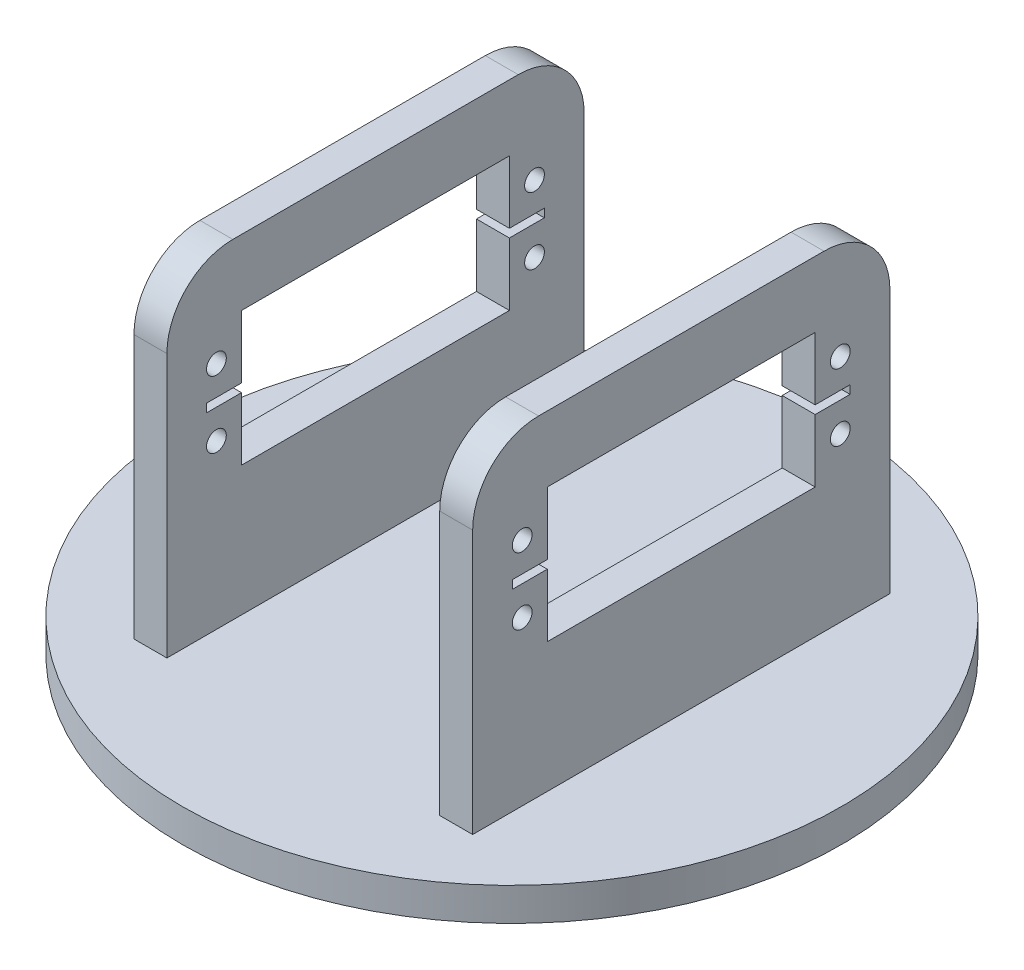
SolidWorks part; units mm, degrees
ref_plane "Front Plane" through (0, 0, 0) normal (0, 0, 1) x (1, 0, 0)
ref_plane "Top Plane" through (0, 0, 0) normal (0, 1, 0) x (1, 0, 0)
ref_plane "Right Plane" through (0, 0, 0) normal (1, 0, 0) x (0, 0, -1)
sketch "Sketch1" plane through (0, 0, 0) normal (0, 1, 0) x (1, 0, 0)
  circle A0 centre (0, 0) radius 50
  circle A1 centre (0, 0) radius 2.778
  dimension "D1" = 100
  dimension "D2" = 5.556
extrude "Boss-Extrude1" add sketch "Sketch1" along normal mid plane 5
sketch "Sketch2" plane through (0, 2.5, 0) normal (0, 1, 0) x (1, 0, 0)
  line L1 (-25.6943, 31.65) -> (-20.6943, 31.65)
  line L2 (-25.6943, 31.65) -> (-25.6943, -31.65)
  line L3 (-25.6943, -31.65) -> (-20.6943, -31.65)
  line L4 (-20.6943, 31.65) -> (-20.6943, -31.65)
  line L5 (-25.6943, 31.65) -> (-20.6943, -31.65) construction
  line L6 (-25.6943, -31.65) -> (-20.6943, 31.65) construction
  point P0 (-23.1943, 0)
  dimension "D1" = 63.3
  dimension "D2" = 5
extrude "Boss-Extrude2" add sketch "Sketch2" along normal blind 50
fillet "Fillet1" radius 10 2 edges at (-23.1943, 52.5, -31.65) (-23.1943, 52.5, 31.65)
sketch "Sketch14" plane through (-20.6943, 0, 0) normal (1, 0, 0) x (0, 0, -1)
  line L0 (-0.01, 72.6962) -> (-0.01, -11.5351) construction
  line L1 (-20.33, 42.5) -> (20.31, 42.5)
  line L2 (-20.33, 42.5) -> (-20.33, 22.18)
  line L3 (-20.33, 22.18) -> (20.31, 22.18)
  line L4 (20.31, 42.5) -> (20.31, 22.18)
  line L5 (-20.33, 42.5) -> (20.31, 22.18) construction
  line L6 (-20.33, 22.18) -> (20.31, 42.5) construction
  line L7 (-25.63, 32.34) -> (-25.63, 32.975)
  line L8 (-25.63, 32.975) -> (-20.33, 32.975)
  line L9 (20.31, 42.5) -> (31.63, 42.5) construction
  line L10 (-31.65, 42.5) -> (-20.33, 42.5) construction
  line L11 (-20.33, 32.975) -> (-20.33, 31.705)
  line L12 (-20.33, 31.705) -> (-25.63, 31.705)
  line L13 (-25.63, 31.705) -> (-25.63, 32.34)
  line L14 (25.61, 31.705) -> (25.61, 32.34)
  line L15 (20.31, 31.705) -> (25.61, 31.705)
  line L16 (20.31, 32.975) -> (20.31, 31.705)
  line L17 (25.61, 32.975) -> (20.31, 32.975)
  line L18 (25.61, 32.34) -> (25.61, 32.975)
  point P0 (-0.01, 32.34)
  dimension "D1" = 40.64
  dimension "D2" = 1.27
  dimension "D3" = 5.3
extrude "Cut-Extrude1" cut sketch "Sketch14" against normal through all contours L4 L1 L2 L3 | L13 L12 L2 L8 L7 | L14 L18 L17 L4 L15
hole_wizard "Ø3.0 (3) Diameter Hole1" positions "Sketch16" profile "Sketch15" hole size "Ø3.0" standard "ISO" end condition through all
sketch "Sketch16" plane through (-20.6943, 0, 0) normal (1, 0, 0) x (0, 0, -1)
  line L0 (20.31, 22.18) -> (20.31, 31.705) construction
  line L1 (-20.33, 42.5) -> (-20.33, 32.975) construction
  line L2 (20.31, 42.5) -> (-20.33, 42.5) construction
  line L3 (-20.33, 22.18) -> (20.31, 22.18) construction
  point P0 (24.12, 37.42)
  point P2 (24.12, 27.26)
  point P4 (-24.14, 37.42)
  point P6 (-24.14, 27.26)
  dimension "D1" = 3.81
  dimension "D2" = 3.81
  dimension "D3" = 5.08
  dimension "D4" = 5.08
sketch "Sketch15" plane through (-20.6943, 37.42, -24.12) normal (0, 1, 0) x (0, 0, -1)
  line L0 (0, 0) -> (0, 29.3057)
  line L1 (0, 29.3057) -> (1.5, 29.3057)
  line L2 (1.5, 29.3057) -> (1.5, 0)
  line L5 (1.5, 0) -> (0, 0)
  line L11 (0, -6.35) -> (0, 107.95) construction
  dimension "Thru Hole Dia." = 3
  dimension "Thru Hole Depth" = 29.3057
mirror "Mirror1" about plane through (0, 0, 0) normal (1, 0, 0) of "Boss-Extrude2", "Fillet1", "Cut-Extrude1", "Ø3.0 (3) Diameter Hole1"
